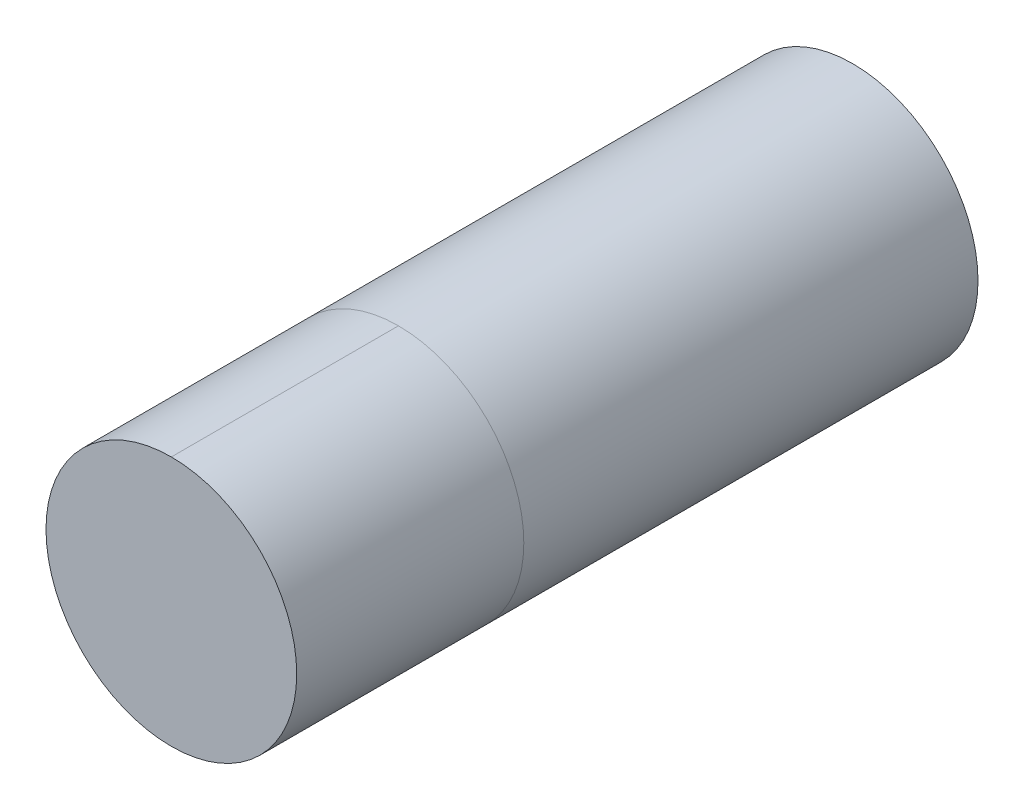
SolidWorks part; units mm, degrees
material "Alloy Steel"
ref_plane "Front Plane" through (0, 0, 0) normal (0, 0, 1) x (1, 0, 0)
ref_plane "Top Plane" through (0, 0, 0) normal (0, 1, 0) x (1, 0, 0)
ref_plane "Right Plane" through (0, 0, 0) normal (1, 0, 0) x (0, 0, -1)
sketch "Sketch1" plane through (0, 0, 0) normal (0, 0, 1) x (1, 0, 0)
  circle A0 centre (0, 0) radius 1.7526
  dimension "D1" = 3.5052
extrude "Boss-Extrude1" add sketch "Sketch1" along normal blind 6.35
sketch "Sketch2" plane through (0, 0, 6.35) normal (0, 0, 1) x (1, 0, 0)
  circle A0 centre (0, 0) radius 1.7526
extrude "Boss-Extrude2" add sketch "Sketch2" along normal blind 3.175 separate body
split line "Split Line1"
